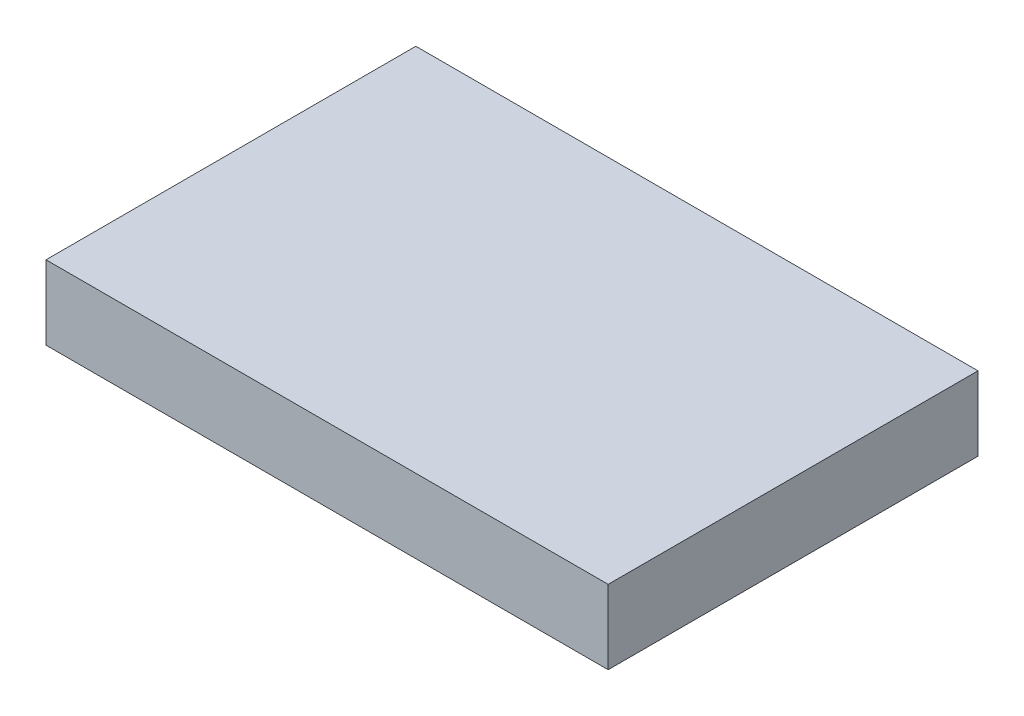
SolidWorks part; units mm, degrees
material "Pure Gold"
ref_plane "Front Plane" through (0, 0, 0) normal (0, 0, 1) x (1, 0, 0)
ref_plane "Top Plane" through (0, 0, 0) normal (0, 1, 0) x (1, 0, 0)
ref_plane "Right Plane" through (0, 0, 0) normal (1, 0, 0) x (0, 0, -1)
sketch "Sketch1" plane through (0, 0, 0) normal (0, 1, 0) x (1, 0, 0)
  line L1 (0, 0) -> (38, 0)
  line L2 (0, 0) -> (0, 25)
  line L3 (0, 25) -> (38, 25)
  line L4 (38, 0) -> (38, 25)
  dimension "D1" = 25
  dimension "D2" = 38
extrude "Boss-Extrude1" add sketch "Sketch1" along normal blind 5
